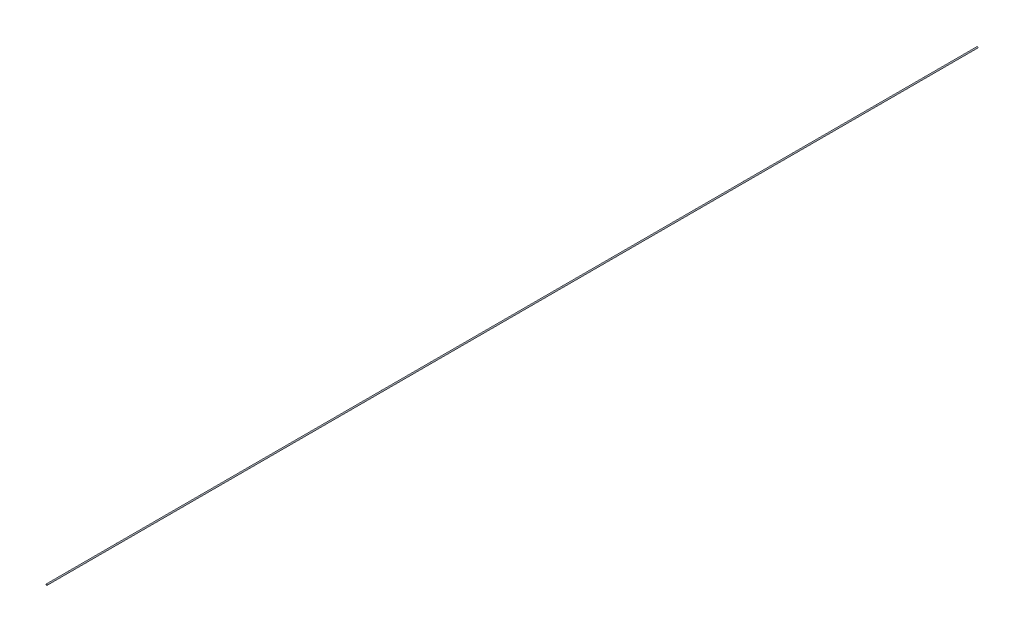
SolidWorks part; units mm, degrees
ref_plane "Front Plane" through (0, 0, 0) normal (0, 0, 1) x (1, 0, 0)
ref_plane "Top Plane" through (0, 0, 0) normal (0, 1, 0) x (1, 0, 0)
ref_plane "Right Plane" through (0, 0, 0) normal (1, 0, 0) x (0, 0, -1)
sketch "Sketch1" plane through (0, 0, 0) normal (0, 0, 1) x (1, 0, 0)
  circle A0 centre (0, 0) radius 0.0625
extrude "Boss-Extrude1" add sketch "Sketch1" along normal blind 100
